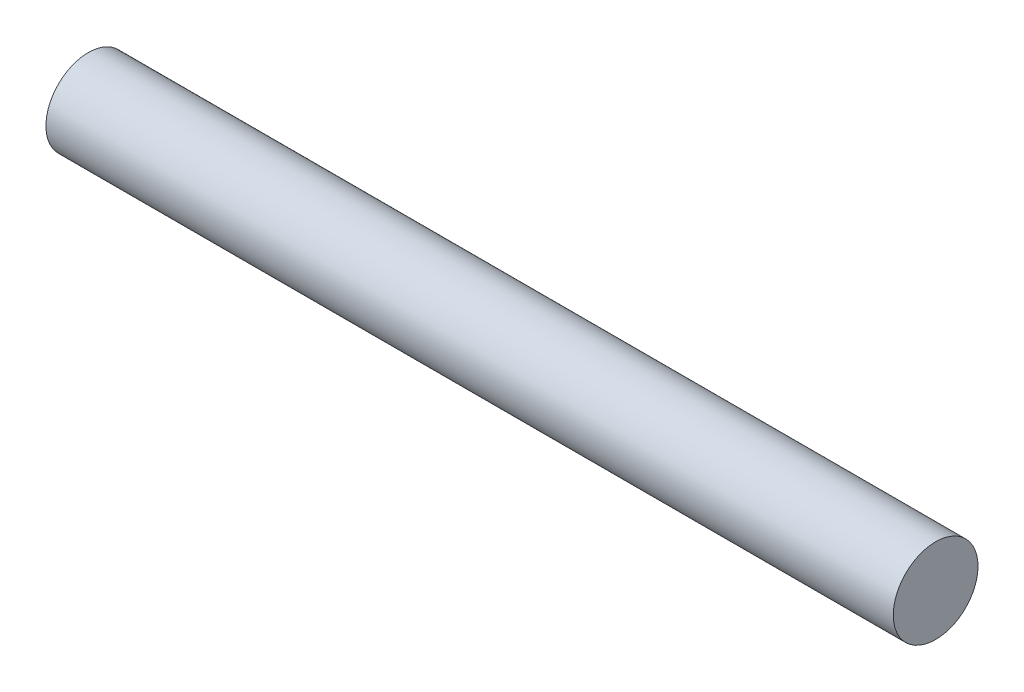
SolidWorks part; units mm, degrees
ref_plane "Front Plane" through (0, 0, 0) normal (0, 0, 1) x (1, 0, 0)
ref_plane "Top Plane" through (0, 0, 0) normal (0, 1, 0) x (1, 0, 0)
ref_plane "Right Plane" through (0, 0, 0) normal (1, 0, 0) x (0, 0, -1)
sketch "Sketch1" plane through (0, 0, 0) normal (1, 0, 0) x (0, 0, -1)
  circle A0 centre (0, 0) radius 9.525
  dimension "D1" = 19.05
extrude "Boss-Extrude1" add sketch "Sketch1" along normal blind 190.5
